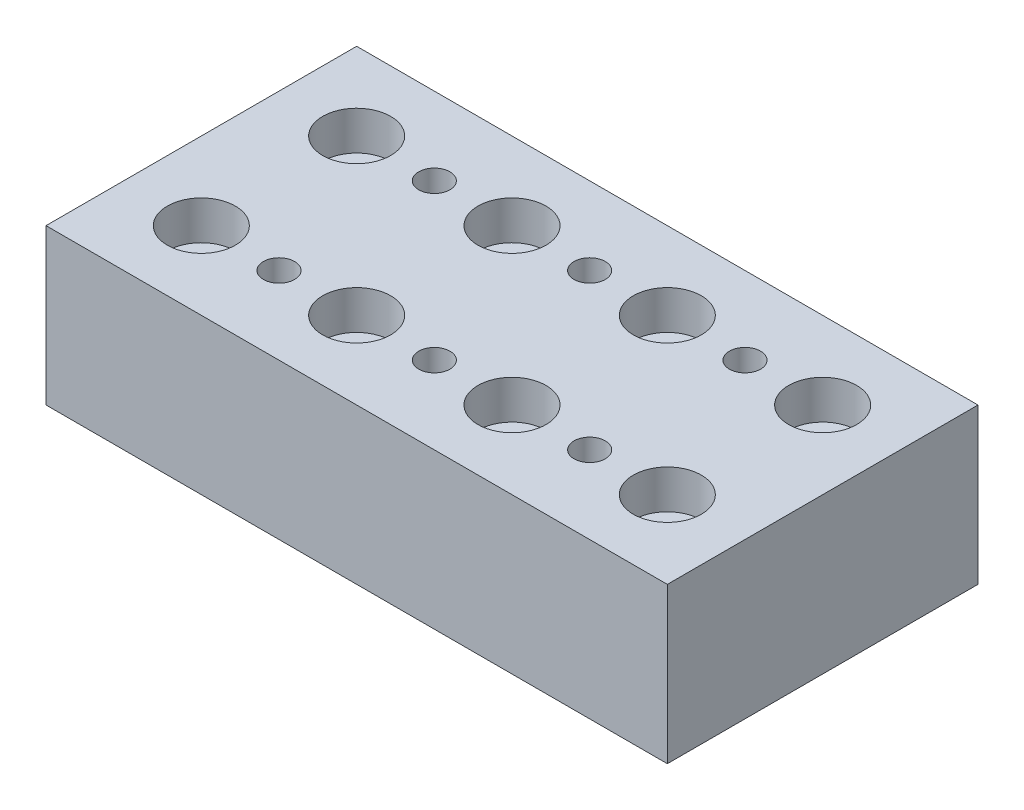
SolidWorks part; units mm, degrees
ref_plane "Front Plane" through (0, 0, 0) normal (0, 0, 1) x (1, 0, 0)
ref_plane "Top Plane" through (0, 0, 0) normal (0, 1, 0) x (1, 0, 0)
ref_plane "Right Plane" through (0, 0, 0) normal (1, 0, 0) x (0, 0, -1)
sketch "Sketch1" plane through (0, 0, 0) normal (0, 1, 0) x (1, 0, 0)
  line L1 (0, 0) -> (101.6, 0)
  line L2 (0, 0) -> (0, 50.8)
  line L3 (0, 50.8) -> (101.6, 50.8)
  line L4 (101.6, 0) -> (101.6, 50.8)
extrude "Boss-Extrude1" add sketch "Sketch1" along normal blind 25.4
hole_wizard "CBORE for 1/4 Socket Head Cap Screw1" positions "Sketch4" profile "Sketch3" counterbore size "1/4" standard "Ansi Inch" end condition through all
sketch "Sketch4" plane through (0, 25.4, 0) normal (0, 1, 0) x (-1, 0, 0)
  point P0 (-12.7, -12.7)
sketch "Sketch3" plane through (12.7, 25.4, -12.7) normal (1, 0, 0) x (0, 0, 1)
  line L0 (0, 0) -> (0, 25.4)
  line L1 (0, 25.4) -> (3.3782, 25.4)
  line L3 (3.3782, 25.4) -> (3.3782, 6.35)
  line L4 (3.3782, 6.35) -> (5.5562, 6.35)
  line L5 (5.5562, 6.35) -> (5.5563, 0)
  line L7 (5.5563, 0) -> (0, 0)
  line L11 (0, -6.35) -> (0, 107.95) construction
  dimension "Thru Hole Dia." = 6.7564
  dimension "Thru Hole Depth" = 25.4
  dimension "C'Bore Dia." = 11.1125
  dimension "C'Bore Depth" = 6.35
pattern_linear "LPattern1" count 2 spacing 25.4 along (0, 0, -1) count 4 spacing 25.4 along (1, 0, 0) of "CBORE for 1/4 Socket Head Cap Screw1"
hole_wizard "1/4-20 Tapped Hole1" positions "Sketch6" profile "Sketch5" tap size "1/4-20" standard "Ansi Inch" end condition through all
sketch "Sketch6" plane through (0, 25.4, 0) normal (0, 1, 0) x (-1, 0, 0)
  point P0 (-25.4, -38.1)
sketch "Sketch5" plane through (25.4, 25.4, -38.1) normal (1, 0, 0) x (0, 0, 1)
  line L0 (0, 0) -> (0, 25.4)
  line L1 (0, 25.4) -> (2.5527, 25.4)
  line L2 (2.5527, 25.4) -> (2.5527, 0)
  line L5 (2.5527, 0) -> (0, 0)
  line L11 (0, -6.35) -> (0, 107.95) construction
  dimension "Thru Tap Drill Dia." = 5.1054
  dimension "Thru Tap Drill Depth" = 25.4
cosmetic thread "Hole Thread1" parameters "D2"=6.35
pattern_linear "LPattern2" count 2 spacing 25.4 along (0, 0, 1) count 3 spacing 25.4 along (1, 0, 0) of "1/4-20 Tapped Hole1"
